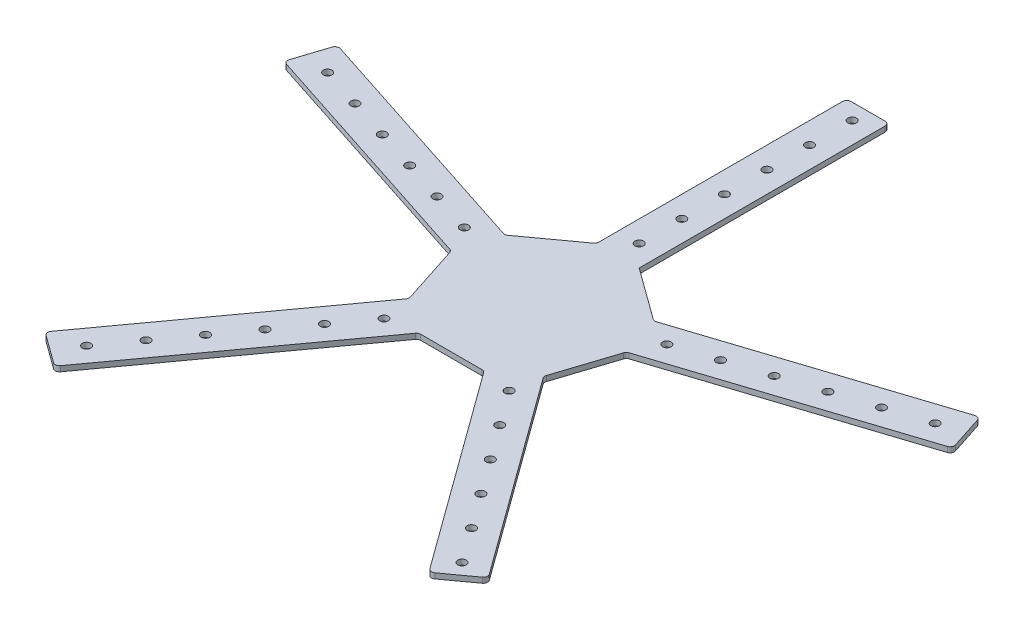
SolidWorks part; units mm, degrees
ref_plane "Front Plane" through (0, 0, 0) normal (0, 0, 1) x (1, 0, 0)
ref_plane "Top Plane" through (0, 0, 0) normal (0, 1, 0) x (1, 0, 0)
ref_plane "Right Plane" through (0, 0, 0) normal (1, 0, 0) x (0, 0, -1)
sketch "Sketch1" plane through (0, 0, 0) normal (0, 1, 0) x (1, 0, 0)
  line L0 (0, 0) -> (0, 50.8) construction
  line L1 (52.2382, 3.6196) -> (44.3892, 27.7765)
  line L2 (12.7, 50.8) -> (-12.7, 50.8)
  line L3 (12.7, 50.8) -> (12.7, 812.8)
  line L4 (12.7, 812.8) -> (-12.7, 812.8)
  line L5 (-12.7, 50.8) -> (-12.7, 812.8)
  line L6 (52.2382, 3.6196) -> (776.9433, 239.0906)
  line L7 (776.9433, 239.0906) -> (769.0942, 263.2474)
  line L8 (44.3892, 27.7765) -> (769.0942, 263.2474)
  line L9 (0, 0) -> (48.3137, 15.6981) construction
  line L10 (19.585, -48.5629) -> (40.134, -33.6332)
  line L11 (19.585, -48.5629) -> (467.4773, -665.0339)
  line L12 (467.4773, -665.0339) -> (488.0264, -650.1041)
  line L13 (40.134, -33.6332) -> (488.0264, -650.1041)
  line L14 (0, 0) -> (29.8595, -41.0981) construction
  line L15 (-40.134, -33.6332) -> (-19.585, -48.5629)
  line L16 (-40.134, -33.6332) -> (-488.0264, -650.1041)
  line L17 (-488.0264, -650.1041) -> (-467.4773, -665.0339)
  line L18 (-19.585, -48.5629) -> (-467.4773, -665.0339)
  line L19 (0, 0) -> (-29.8595, -41.0981) construction
  line L20 (-44.3892, 27.7765) -> (-52.2382, 3.6196)
  line L21 (-44.3892, 27.7765) -> (-769.0942, 263.2474)
  line L22 (-769.0942, 263.2474) -> (-776.9433, 239.0906)
  line L23 (-52.2382, 3.6196) -> (-776.9433, 239.0906)
  line L24 (0, 0) -> (-48.3137, 15.6981) construction
  circle A0 centre (0, 63.5) radius 2.54
  circle A1 centre (0, 88.9) radius 2.54
  circle A2 centre (0, 114.3) radius 2.54
  circle A3 centre (0, 139.7) radius 2.54
  circle A4 centre (0, 165.1) radius 2.54
  circle A5 centre (0, 190.5) radius 2.54
  circle A6 centre (0, 215.9) radius 2.54
  circle A7 centre (0, 241.3) radius 2.54
  circle A8 centre (0, 266.7) radius 2.54
  circle A9 centre (0, 292.1) radius 2.54
  circle A10 centre (0, 317.5) radius 2.54
  circle A11 centre (0, 342.9) radius 2.54
  circle A12 centre (0, 368.3) radius 2.54
  circle A13 centre (0, 393.7) radius 2.54
  circle A14 centre (0, 419.1) radius 2.54
  circle A15 centre (0, 444.5) radius 2.54
  circle A16 centre (0, 469.9) radius 2.54
  circle A17 centre (0, 495.3) radius 2.54
  circle A18 centre (0, 520.7) radius 2.54
  circle A19 centre (0, 546.1) radius 2.54
  circle A20 centre (0, 571.5) radius 2.54
  circle A21 centre (0, 596.9) radius 2.54
  circle A22 centre (0, 622.3) radius 2.54
  circle A23 centre (0, 647.7) radius 2.54
  circle A24 centre (0, 673.1) radius 2.54
  circle A25 centre (0, 698.5) radius 2.54
  circle A26 centre (0, 723.9) radius 2.54
  circle A27 centre (0, 749.3) radius 2.54
  circle A28 centre (0, 774.7) radius 2.54
  circle A29 centre (0, 800.1) radius 2.54
  circle A30 centre (60.3921, 19.6226) radius 2.54
  circle A31 centre (84.5489, 27.4716) radius 2.54
  circle A32 centre (108.7058, 35.3206) radius 2.54
  circle A33 centre (132.8626, 43.1697) radius 2.54
  circle A34 centre (157.0194, 51.0187) radius 2.54
  circle A35 centre (181.1763, 58.8677) radius 2.54
  circle A36 centre (205.3331, 66.7168) radius 2.54
  circle A37 centre (229.4899, 74.5658) radius 2.54
  circle A38 centre (253.6468, 82.4148) radius 2.54
  circle A39 centre (277.8036, 90.2639) radius 2.54
  circle A40 centre (301.9604, 98.1129) radius 2.54
  circle A41 centre (326.1173, 105.9619) radius 2.54
  circle A42 centre (350.2741, 113.811) radius 2.54
  circle A43 centre (374.431, 121.66) radius 2.54
  circle A44 centre (398.5878, 129.509) radius 2.54
  circle A45 centre (422.7446, 137.3581) radius 2.54
  circle A46 centre (446.9015, 145.2071) radius 2.54
  circle A47 centre (471.0583, 153.0561) radius 2.54
  circle A48 centre (495.2151, 160.9051) radius 2.54
  circle A49 centre (519.372, 168.7542) radius 2.54
  circle A50 centre (543.5288, 176.6032) radius 2.54
  circle A51 centre (567.6856, 184.4522) radius 2.54
  circle A52 centre (591.8425, 192.3013) radius 2.54
  circle A53 centre (615.9993, 200.1503) radius 2.54
  circle A54 centre (640.1561, 207.9993) radius 2.54
  circle A55 centre (664.313, 215.8484) radius 2.54
  circle A56 centre (688.4698, 223.6974) radius 2.54
  circle A57 centre (712.6266, 231.5464) radius 2.54
  circle A58 centre (736.7835, 239.3955) radius 2.54
  circle A59 centre (760.9403, 247.2445) radius 2.54
  circle A60 centre (37.3244, -51.3726) radius 2.54
  circle A61 centre (52.2541, -71.9216) radius 2.54
  circle A62 centre (67.1839, -92.4706) radius 2.54
  circle A63 centre (82.1136, -113.0197) radius 2.54
  circle A64 centre (97.0433, -133.5687) radius 2.54
  circle A65 centre (111.9731, -154.1177) radius 2.54
  circle A66 centre (126.9028, -174.6668) radius 2.54
  circle A67 centre (141.8326, -195.2158) radius 2.54
  circle A68 centre (156.7623, -215.7648) radius 2.54
  circle A69 centre (171.6921, -236.3139) radius 2.54
  circle A70 centre (186.6218, -256.8629) radius 2.54
  circle A71 centre (201.5516, -277.4119) radius 2.54
  circle A72 centre (216.4813, -297.961) radius 2.54
  circle A73 centre (231.4111, -318.51) radius 2.54
  circle A74 centre (246.3408, -339.059) radius 2.54
  circle A75 centre (261.2705, -359.6081) radius 2.54
  circle A76 centre (276.2003, -380.1571) radius 2.54
  circle A77 centre (291.13, -400.7061) radius 2.54
  circle A78 centre (306.0598, -421.2551) radius 2.54
  circle A79 centre (320.9895, -441.8042) radius 2.54
  circle A80 centre (335.9193, -462.3532) radius 2.54
  circle A81 centre (350.849, -482.9022) radius 2.54
  circle A82 centre (365.7788, -503.4513) radius 2.54
  circle A83 centre (380.7085, -524.0003) radius 2.54
  circle A84 centre (395.6383, -544.5493) radius 2.54
  circle A85 centre (410.568, -565.0984) radius 2.54
  circle A86 centre (425.4977, -585.6474) radius 2.54
  circle A87 centre (440.4275, -606.1964) radius 2.54
  circle A88 centre (455.3572, -626.7455) radius 2.54
  circle A89 centre (470.287, -647.2945) radius 2.54
  circle A90 centre (-37.3244, -51.3726) radius 2.54
  circle A91 centre (-52.2541, -71.9216) radius 2.54
  circle A92 centre (-67.1839, -92.4706) radius 2.54
  circle A93 centre (-82.1136, -113.0197) radius 2.54
  circle A94 centre (-97.0433, -133.5687) radius 2.54
  circle A95 centre (-111.9731, -154.1177) radius 2.54
  circle A96 centre (-126.9028, -174.6668) radius 2.54
  circle A97 centre (-141.8326, -195.2158) radius 2.54
  circle A98 centre (-156.7623, -215.7648) radius 2.54
  circle A99 centre (-171.6921, -236.3139) radius 2.54
  circle A100 centre (-186.6218, -256.8629) radius 2.54
  circle A101 centre (-201.5516, -277.4119) radius 2.54
  circle A102 centre (-216.4813, -297.961) radius 2.54
  circle A103 centre (-231.4111, -318.51) radius 2.54
  circle A104 centre (-246.3408, -339.059) radius 2.54
  circle A105 centre (-261.2705, -359.6081) radius 2.54
  circle A106 centre (-276.2003, -380.1571) radius 2.54
  circle A107 centre (-291.13, -400.7061) radius 2.54
  circle A108 centre (-306.0598, -421.2551) radius 2.54
  circle A109 centre (-320.9895, -441.8042) radius 2.54
  circle A110 centre (-335.9193, -462.3532) radius 2.54
  circle A111 centre (-350.849, -482.9022) radius 2.54
  circle A112 centre (-365.7788, -503.4513) radius 2.54
  circle A113 centre (-380.7085, -524.0003) radius 2.54
  circle A114 centre (-395.6383, -544.5493) radius 2.54
  circle A115 centre (-410.568, -565.0984) radius 2.54
  circle A116 centre (-425.4977, -585.6474) radius 2.54
  circle A117 centre (-440.4275, -606.1964) radius 2.54
  circle A118 centre (-455.3572, -626.7455) radius 2.54
  circle A119 centre (-470.287, -647.2945) radius 2.54
  circle A120 centre (-60.3921, 19.6226) radius 2.54
  circle A121 centre (-84.5489, 27.4716) radius 2.54
  circle A122 centre (-108.7058, 35.3206) radius 2.54
  circle A123 centre (-132.8626, 43.1697) radius 2.54
  circle A124 centre (-157.0194, 51.0187) radius 2.54
  circle A125 centre (-181.1763, 58.8677) radius 2.54
  circle A126 centre (-205.3331, 66.7168) radius 2.54
  circle A127 centre (-229.4899, 74.5658) radius 2.54
  circle A128 centre (-253.6468, 82.4148) radius 2.54
  circle A129 centre (-277.8036, 90.2639) radius 2.54
  circle A130 centre (-301.9604, 98.1129) radius 2.54
  circle A131 centre (-326.1173, 105.9619) radius 2.54
  circle A132 centre (-350.2741, 113.811) radius 2.54
  circle A133 centre (-374.431, 121.66) radius 2.54
  circle A134 centre (-398.5878, 129.509) radius 2.54
  circle A135 centre (-422.7446, 137.3581) radius 2.54
  circle A136 centre (-446.9015, 145.2071) radius 2.54
  circle A137 centre (-471.0583, 153.0561) radius 2.54
  circle A138 centre (-495.2151, 160.9051) radius 2.54
  circle A139 centre (-519.372, 168.7542) radius 2.54
  circle A140 centre (-543.5288, 176.6032) radius 2.54
  circle A141 centre (-567.6856, 184.4522) radius 2.54
  circle A142 centre (-591.8425, 192.3013) radius 2.54
  circle A143 centre (-615.9993, 200.1503) radius 2.54
  circle A144 centre (-640.1561, 207.9993) radius 2.54
  circle A145 centre (-664.313, 215.8484) radius 2.54
  circle A146 centre (-688.4698, 223.6974) radius 2.54
  circle A147 centre (-712.6266, 231.5464) radius 2.54
  circle A148 centre (-736.7835, 239.3955) radius 2.54
  circle A149 centre (-760.9403, 247.2445) radius 2.54
  point P329 (0, 0)
  dimension "D5" = 5.08
  dimension "D6" = 12.7
  dimension "D7" = 12.7
  dimension "D1" = 50.8
  dimension "D2" = 762
  dimension "D3" = 25.4
  dimension "D4" = 12.7
  dimension "D8" = 30
  dimension "D9" = 5
ref_plane "Plane1" through (0, 0, 0) normal (0, 1, 0) x (1, 0, 0)
sketch "Sketch2" plane through (0, 0, 0) normal (0, 1, 0) x (1, 0, 0)
  line L0 (-12.7, 52.0942) -> (-12.7, 197.4511)
  line L1 (-12.7, 50.8) -> (-12.7, 812.8) construction
  line L2 (-10.16, 199.9911) -> (10.16, 199.9911)
  line L3 (12.7, 50.8) -> (12.7, 812.8) construction
  line L4 (12.7, 197.4511) -> (12.7, 50.8)
  line L5 (12.7, 50.8) -> (43.3421, 28.5372)
  line L6 (45.62, 28.1764) -> (188.8815, 74.7249)
  line L7 (44.3892, 27.7765) -> (769.0942, 263.2474) construction
  line L8 (192.0821, 73.0941) -> (198.3613, 53.7687)
  line L9 (52.2382, 3.6196) -> (776.9433, 239.0906) construction
  line L10 (196.7306, 50.5681) -> (53.469, 4.0196)
  line L11 (51.8383, 2.3888) -> (40.5339, -32.4023)
  line L12 (40.8947, -34.6802) -> (126.1782, -152.0628)
  line L13 (40.134, -33.6332) -> (488.0264, -650.1041) construction
  line L14 (125.6163, -155.6107) -> (109.177, -167.5545)
  line L15 (19.585, -48.5629) -> (467.4773, -665.0339) construction
  line L16 (105.6291, -166.9926) -> (20.3457, -49.61)
  line L17 (18.2908, -48.5629) -> (-18.2908, -48.5629)
  line L18 (-20.3457, -49.61) -> (-109.4177, -172.207)
  line L19 (-19.585, -48.5629) -> (-467.4773, -665.0339) construction
  line L20 (-112.9655, -172.7689) -> (-129.4048, -160.8251)
  line L21 (-40.134, -33.6332) -> (-488.0264, -650.1041) construction
  line L22 (-129.9667, -157.2773) -> (-40.8947, -34.6802)
  line L23 (-40.5339, -32.4023) -> (-51.8383, 2.3888)
  line L24 (-53.469, 4.0196) -> (-197.6236, 50.8582)
  line L25 (-52.2382, 3.6196) -> (-776.9433, 239.0906) construction
  line L26 (-199.2544, 54.0588) -> (-192.9752, 73.3843)
  line L27 (-44.3892, 27.7765) -> (-769.0942, 263.2474) construction
  line L28 (-189.7746, 75.0151) -> (-45.62, 28.1764)
  line L29 (-43.3421, 28.5372) -> (-13.747, 50.0393)
  arc A0 (-129.4048, -160.8251) -> (-129.9667, -157.2773) centre (-127.9118, -158.7702) cw
  arc A1 (-109.4177, -172.207) -> (-112.9655, -172.7689) centre (-111.4726, -170.714) cw
  arc A2 (109.177, -167.5545) -> (105.6291, -166.9926) centre (107.6841, -165.4996) cw
  arc A3 (126.1782, -152.0628) -> (125.6163, -155.6107) centre (124.1233, -153.5558) cw
  arc A4 (198.3613, 53.7687) -> (196.7306, 50.5681) centre (195.9457, 52.9837) cw
  arc A5 (188.8815, 74.7249) -> (192.0821, 73.0941) centre (189.6664, 72.3092) cw
  arc A6 (43.3421, 28.5372) -> (45.62, 28.1764) centre (44.8351, 30.5921) ccw
  arc A7 (53.469, 4.0196) -> (51.8383, 2.3888) centre (54.2539, 1.6039) ccw
  arc A8 (40.5339, -32.4023) -> (40.8947, -34.6802) centre (42.9496, -33.1872) ccw
  arc A9 (20.3457, -49.61) -> (18.2908, -48.5629) centre (18.2908, -51.1029) ccw
  arc A10 (-18.2908, -48.5629) -> (-20.3457, -49.61) centre (-18.2908, -51.1029) ccw
  arc A11 (-40.8947, -34.6802) -> (-40.5339, -32.4023) centre (-42.9496, -33.1872) ccw
  arc A12 (-192.9752, 73.3843) -> (-189.7746, 75.0151) centre (-190.5595, 72.5994) cw
  arc A13 (-51.8383, 2.3888) -> (-53.469, 4.0196) centre (-54.2539, 1.6039) ccw
  arc A14 (-197.6236, 50.8582) -> (-199.2544, 54.0588) centre (-196.8387, 53.2739) cw
  arc A15 (-45.62, 28.1764) -> (-43.3421, 28.5372) centre (-44.8351, 30.5921) ccw
  arc A16 (-12.7, 52.0942) -> (-13.747, 50.0393) centre (-15.24, 52.0942) cw
  arc A17 (-12.7, 197.4511) -> (-10.16, 199.9911) centre (-10.16, 197.4511) cw
  arc A18 (10.16, 199.9911) -> (12.7, 197.4511) centre (10.16, 197.4511) cw
  point P52 (-131.4597, -159.3322)
  point P55 (-110.9106, -174.2619)
  point P58 (107.1221, -169.0475)
  point P61 (127.6712, -154.1177)
  point P64 (199.1462, 51.353)
  point P67 (191.2972, 75.5098)
  point P70 (44.3892, 27.7765)
  point P73 (52.2382, 3.6196)
  point P76 (40.134, -33.6332)
  point P79 (19.585, -48.5629)
  point P82 (-19.585, -48.5629)
  point P85 (-40.134, -33.6332)
  point P88 (-192.1903, 75.8)
  point P91 (-52.2382, 3.6196)
  point P94 (-200.0393, 51.6431)
  point P97 (-44.3892, 27.7765)
  point P100 (-12.7, 50.8)
  point P103 (-12.7, 199.9911)
  point P106 (12.7, 199.9911)
  dimension "D1" = 2.54
extrude "Boss-Extrude1" add sketch "Sketch2" along normal blind 3.175
sketch "Sketch4" plane through (0, 0, 0) normal (0, 1, 0) x (1, 0, 0)
  circle A0 centre (0, 63.5) radius 2.54
  circle A1 centre (60.3921, 19.6226) radius 2.54
  circle A2 centre (37.3244, -51.3726) radius 2.54
  circle A3 centre (-37.3244, -51.3726) radius 2.54
  circle A4 centre (-60.3921, 19.6226) radius 2.54
  circle A5 centre (0, 88.9) radius 2.54
  circle A6 centre (0, 114.3) radius 2.54
  circle A7 centre (0, 139.7) radius 2.54
  circle A8 centre (0, 165.1) radius 2.54
  circle A9 centre (0, 190.5) radius 2.54
  circle A10 centre (84.5489, 27.4716) radius 2.54
  circle A11 centre (108.7058, 35.3206) radius 2.54
  circle A12 centre (132.8626, 43.1697) radius 2.54
  circle A13 centre (157.0194, 51.0187) radius 2.54
  circle A14 centre (181.1763, 58.8677) radius 2.54
  circle A15 centre (52.2541, -71.9216) radius 2.54
  circle A16 centre (67.1839, -92.4706) radius 2.54
  circle A17 centre (82.1136, -113.0197) radius 2.54
  circle A18 centre (97.0433, -133.5687) radius 2.54
  circle A19 centre (111.9731, -154.1177) radius 2.54
  circle A20 centre (-52.2541, -71.9216) radius 2.54
  circle A21 centre (-67.1839, -92.4706) radius 2.54
  circle A22 centre (-82.1136, -113.0197) radius 2.54
  circle A23 centre (-97.0433, -133.5687) radius 2.54
  circle A24 centre (-111.9731, -154.1177) radius 2.54
  circle A25 centre (-84.5489, 27.4716) radius 2.54
  circle A26 centre (-108.7058, 35.3206) radius 2.54
  circle A27 centre (-132.8626, 43.1697) radius 2.54
  circle A28 centre (-157.0194, 51.0187) radius 2.54
  circle A29 centre (-181.1763, 58.8677) radius 2.54
  dimension "D1" = 5.08
  dimension "D2" = 5.08
  dimension "D3" = 5.08
  dimension "D4" = 5.08
  dimension "D5" = 5.08
  dimension "D7" = 25.4
  dimension "D12" = 25.4
  dimension "D13" = 25.4
  dimension "D14" = 25.4
  dimension "D15" = 25.4
  dimension "D6" = 6
  dimension "D8" = 6
  dimension "D9" = 6
  dimension "D10" = 6
  dimension "D11" = 6
extrude "Cut-Extrude12" cut sketch "Sketch4" along normal blind 3.175
